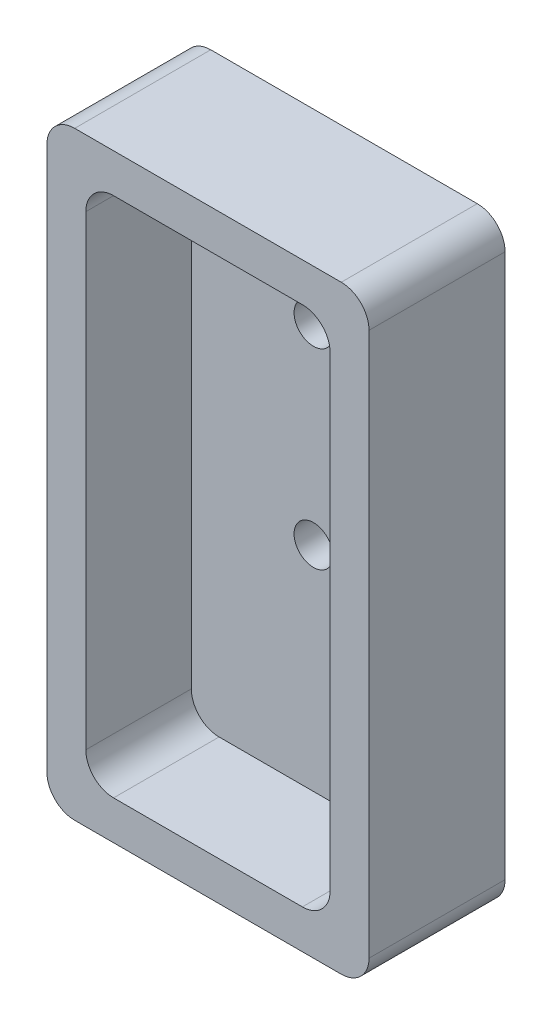
SolidWorks part; units mm, degrees
ref_plane "Front" through (0, 0, 0) normal (0, 0, 1) x (1, 0, 0)
ref_plane "Top" through (0, 0, 0) normal (0, 1, 0) x (1, 0, 0)
ref_plane "Right" through (0, 0, 0) normal (1, 0, 0) x (0, 0, -1)
sketch "Esboço1" plane through (0, 0, 0) normal (0, 1, 0) x (1, 0, 0)
  line L0 (-29, 12.25) -> (29, -12.25) construction
  line L1 (-29, 12.25) -> (29, 12.25)
  line L2 (-29, 12.25) -> (-29, -12.25)
  line L3 (-29, -12.25) -> (29, -12.25)
  line L4 (29, 12.25) -> (29, -12.25)
  line L5 (-29, -12.25) -> (29, 12.25) construction
  point P4 (0, 0)
  dimension "D1" = 24.5
  dimension "D2" = 58
extrude "Ressalto-extrusão1" add sketch "Esboço1" along normal blind 107.92
fillet "Filete1" radius 5 4 edges at (29, 0, 0) (-29, 0, 0) (-29, 107.92, 0) (29, 107.92, 0)
sketch "Esboço2" plane through (0, 0, 12.25) normal (0, 0, 1) x (1, 0, 0)
  line L8 (-22, 7) -> (22, 7)
  line L9 (22, 7) -> (22, 100.92)
  line L10 (22, 100.92) -> (-22, 100.92)
  line L11 (-22, 100.92) -> (-22, 7)
  line L12 (-22, 7) -> (22, 7)
  line L13 (22, 7) -> (22, 100.92)
  line L14 (22, 100.92) -> (-22, 100.92)
  line L15 (-22, 100.92) -> (-22, 7)
  dimension "D1" = 7
extrude "Corte-extrusão1" cut sketch "Esboço2" against normal blind 19 contours L12 L13 L14 L15
fillet "Filete2" radius 5 4 edges at (22, 7, 2.75) (-22, 7, 2.75) (22, 100.92, 2.75) (-22, 100.92, 2.75)
sketch "Esboço3" plane through (0, 0, -6.75) normal (0, 0, 1) x (1, 0, 0)
  line L0 (17, 100.92) -> (-17, 100.92) construction
  line L1 (17, 100.92) -> (-17, 100.92) construction
  circle A0 centre (0, 79.92) radius 3.5
  circle A1 centre (0, 45.4387) radius 3.5
  point P5 (0, 100.92)
  dimension "D1" = 21
  dimension "D2" = 34.4813
  dimension "D3" = 7
extrude "Corte-extrusão2" cut sketch "Esboço3" against normal through all both and the other way through all
